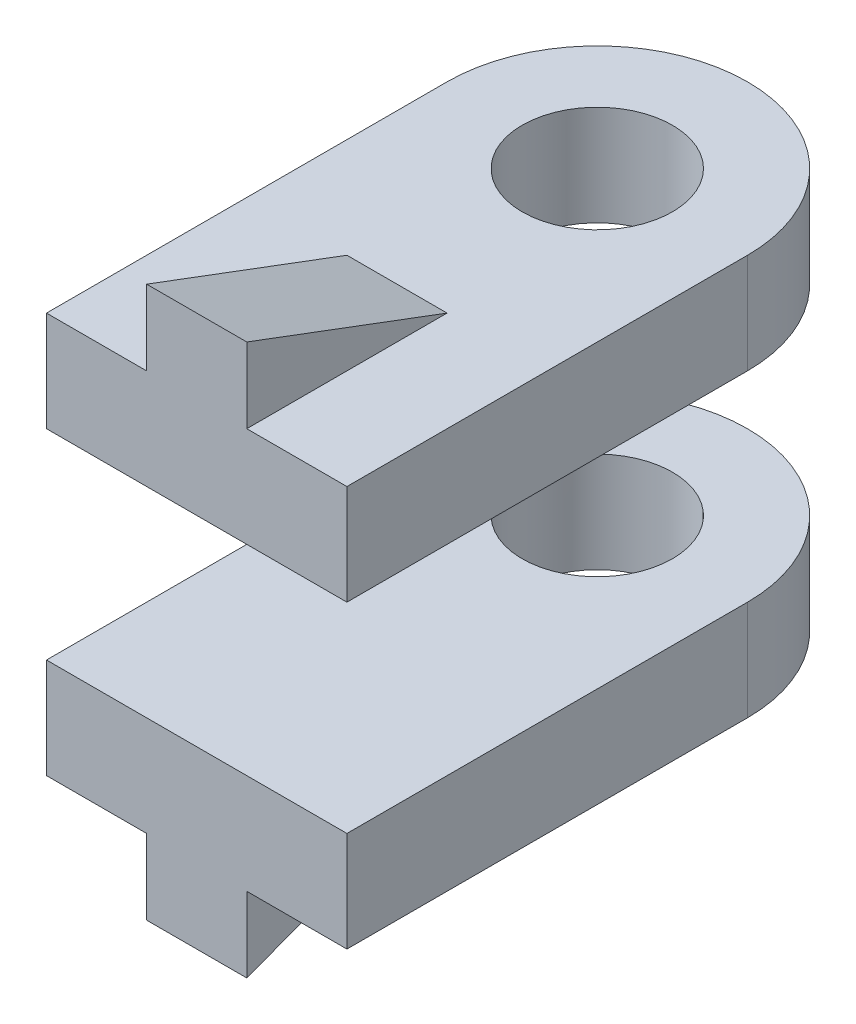
SolidWorks part; units mm, degrees
ref_plane "前视基准面" through (0, 0, 0) normal (0, 0, 1) x (1, 0, 0)
ref_plane "上视基准面" through (0, 0, 0) normal (0, 1, 0) x (1, 0, 0)
ref_plane "右视基准面" through (0, 0, 0) normal (1, 0, 0) x (0, 0, -1)
sketch "草图1" plane through (0, 0, 0) normal (0, 1, 0) x (1, 0, 0)
  line L0 (-102.3935, 0) -> (101.7335, 0) construction
  line L1 (0, 84.4691) -> (0, -80.2928) construction
  line L2 (-30, 0) -> (-30, 80)
  line L3 (-30, 0) -> (30, 0)
  line L4 (30, 0) -> (30, 80)
  arc A0 (-30, 80) -> (30, 80) centre (0, 80) cw
  circle A1 centre (0, 80) radius 15
  dimension "D1" = 30
  dimension "D2" = 30
  dimension "D3" = 80
  dimension "D4" = 30
extrude "凸台-拉伸2" add sketch "草图1" along normal mid plane 80
sketch "草图2" plane through (0, 0, 0) normal (0, 0, 1) x (1, 0, 0)
  line L0 (0, -53.3094) -> (0, 63.9589) construction
  line L1 (-53.1046, 0) -> (54.7327, 0) construction
  line L2 (-30, -20) -> (30, -20)
  line L3 (-30, 40) -> (-30, -40) construction
  line L4 (30, 40) -> (30, -40) construction
  line L5 (30, -20) -> (30, 20)
  line L6 (30, 20) -> (-30, 20)
  line L7 (-30, 20) -> (-30, -20)
  dimension "D1" = 20
  dimension "D2" = 20
extrude "切除-拉伸1" cut sketch "草图2" against normal blind 110
sketch "草图3" plane through (0, 0, 0) normal (1, 0, 0) x (0, 0, -1)
  line L0 (0, 40) -> (0, 55)
  line L1 (0, 55) -> (40, 40)
  line L2 (0, 40) -> (80, 40) construction
  line L3 (40, 40) -> (0, 40)
  line L4 (0, -40) -> (0, -55)
  line L5 (0, -55) -> (40, -40)
  line L6 (0, -40) -> (80, -40) construction
  line L7 (40, -40) -> (0, -40)
  line L8 (0, -40) -> (-0.4076, -39.7976)
  dimension "D1" = 15
  dimension "D2" = 40
  dimension "D3" = 40
  dimension "D4" = 15
extrude "凸台-拉伸3" add sketch "草图3" against normal mid plane 20 contours L5 L7 L4 | L1 L3 L0
